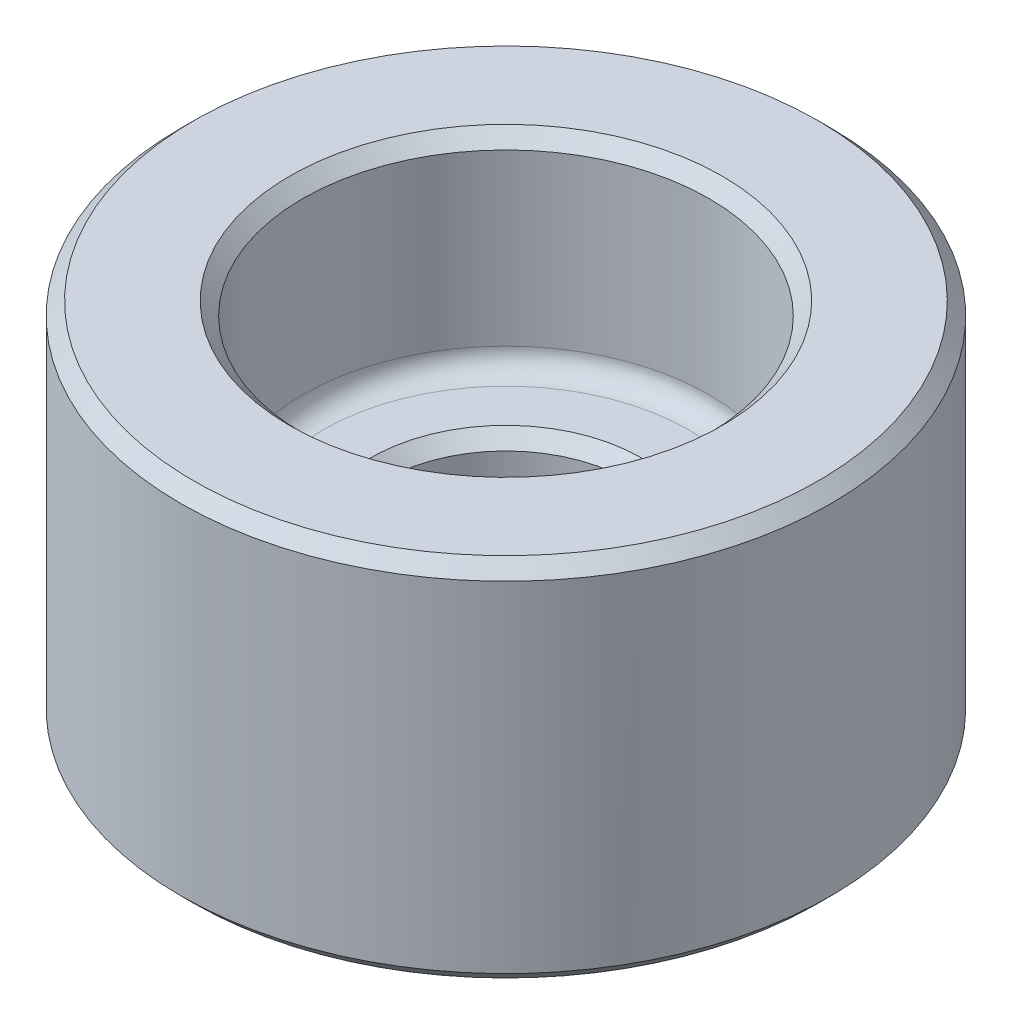
SolidWorks part; units mm, degrees
material "Oynx"
ref_plane "Front" through (0, 0, 0) normal (0, 0, 1) x (1, 0, 0)
ref_plane "Top" through (0, 0, 0) normal (0, 1, 0) x (1, 0, 0)
ref_plane "Right" through (0, 0, 0) normal (1, 0, 0) x (0, 0, -1)
sketch "Sketch1" plane through (0, 0, 0) normal (0, 0, 1) x (1, 0, 0)
  line L0 (2.3813, 0) -> (2.3813, 3.175)
  line L1 (2.3813, 3.175) -> (3.9688, 3.175)
  line L2 (3.9688, 3.175) -> (3.9688, 7.1437)
  line L3 (3.9688, 7.1437) -> (6.35, 7.1437)
  line L4 (6.35, 7.1437) -> (6.35, 0)
  line L5 (6.35, 0) -> (2.3813, 0)
  line L6 (0, 0) -> (0, -94.7854) construction
  dimension "D1" = 4.7625
  dimension "D2" = 3.175
  dimension "D3" = 7.9375
  dimension "D4" = 12.7
  dimension "D5" = 3.9688
revolve "Revolve1" add sketch "Sketch1" angle 360 about L6
fillet "Fillet1" radius 0.3969 1 edges at (0, 3.175, 3.9688)
chamfer "Chamfer1" distance 0.254 angle 45 5 edges at (0, 7.1437, 3.9688) (0, 0, 6.35) (0, 7.1437, 6.35) (0, 3.175, 2.3813) (0, 0, 2.3813)
